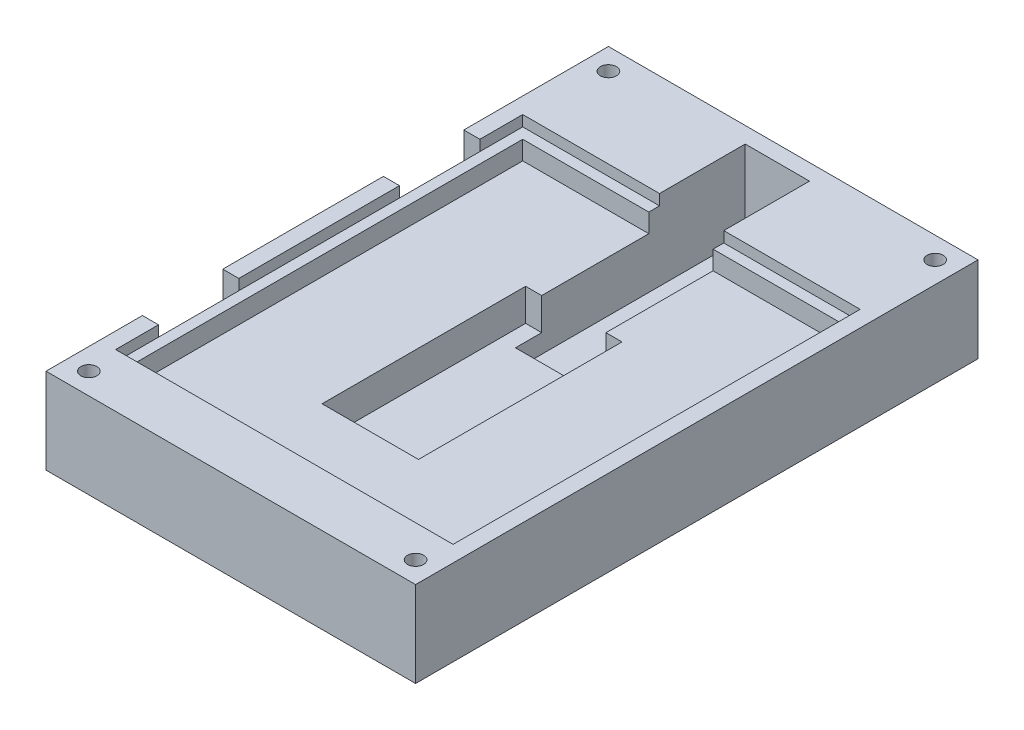
SolidWorks part; units mm, degrees
ref_plane "Front Plane" through (0, 0, 0) normal (0, 0, 1) x (1, 0, 0)
ref_plane "Top Plane" through (0, 0, 0) normal (0, 1, 0) x (1, 0, 0)
ref_plane "Right Plane" through (0, 0, 0) normal (1, 0, 0) x (0, 0, -1)
sketch "Sketch1" plane through (0, 0, 0) normal (0, 1, 0) x (1, 0, 0)
  line L1 (0, 0) -> (69, 0)
  line L2 (0, 0) -> (0, 105)
  line L3 (0, 105) -> (69, 105)
  line L4 (69, 0) -> (69, 105)
  dimension "D1" = 69
  dimension "D2" = 105
extrude "Boss-Extrude1" add sketch "Sketch1" along normal blind 16
sketch "Sketch2" plane through (0, 16, 0) normal (0, 1, 0) x (1, 0, 0)
  line L0 (0, 105) -> (0, 0) construction
  line L1 (3, 86) -> (66, 86)
  line L2 (3, 86) -> (3, 10)
  line L3 (3, 10) -> (66, 10)
  line L4 (66, 86) -> (66, 10)
  line L5 (0, 0) -> (69, 0) construction
  dimension "D1" = 63
  dimension "D2" = 76
  dimension "D3" = 3
  dimension "D4" = 10
extrude "Cut-Extrude1" cut sketch "Sketch2" against normal blind 2
sketch "Sketch3" plane through (0, 14, 0) normal (0, 1, 0) x (1, 0, 0)
  line L0 (3, 86) -> (3, 10) construction
  line L1 (5, 84) -> (64, 84)
  line L2 (5, 84) -> (5, 12)
  line L3 (5, 12) -> (64, 12)
  line L4 (64, 84) -> (64, 12)
  line L5 (66, 10) -> (66, 86) construction
  line L6 (66, 86) -> (3, 86) construction
  line L7 (3, 10) -> (66, 10) construction
  dimension "D1" = 2
  dimension "D2" = 2
  dimension "D3" = 2
  dimension "D4" = 2
extrude "Cut-Extrude2" cut sketch "Sketch3" against normal blind 3.5
sketch "Sketch4" plane through (0, 10.5, 0) normal (0, 1, 0) x (1, 0, 0)
  line L0 (64, 84) -> (5, 84) construction
  line L1 (25.54, 64) -> (43.54, 64)
  line L2 (25.54, 64) -> (25.54, 26)
  line L3 (25.54, 26) -> (43.54, 26)
  line L4 (43.54, 64) -> (43.54, 26)
  line L5 (64, 12) -> (64, 84) construction
  dimension "D1" = 18
  dimension "D2" = 38
  dimension "D3" = 20
  dimension "D4" = 20.46
extrude "Cut-Extrude3" cut sketch "Sketch4" against normal blind 6 contours L2 L3 L4 L1
sketch "Sketch5" plane through (0, 10.5, 0) normal (0, 1, 0) x (1, 0, 0)
  line L1 (28.54, 90.5747) -> (28.54, 59.1011)
  line L2 (28.54, 59.1011) -> (40.54, 59.1011)
  line L3 (40.54, 90.5747) -> (28.54, 90.5747)
  line L4 (40.54, 59.1011) -> (40.54, 90.5747)
  dimension "D1" = 12
extrude "Cut-Extrude4" cut sketch "Sketch5" against normal blind 9.5
sketch "Sketch6" plane through (0, 16, 0) normal (0, 1, 0) x (1, 0, 0)
  line L0 (69, 105) -> (0, 105) construction
  line L1 (28.54, 102) -> (40.54, 102)
  line L2 (28.54, 102) -> (28.54, 84)
  line L3 (28.54, 84) -> (40.54, 84)
  line L4 (40.54, 102) -> (40.54, 84)
  dimension "D1" = 3
extrude "Cut-Extrude5" cut sketch "Sketch6" against normal blind 15
sketch "Sketch7" plane through (0, 16, 0) normal (0, 1, 0) x (1, 0, 0)
  line L0 (0, 0) -> (69, 0) construction
  line L1 (0, 105) -> (0, 0) construction
  line L2 (69, 0) -> (69, 105) construction
  line L3 (69, 105) -> (0, 105) construction
  circle A0 centre (4, 4) radius 1.5
  circle A1 centre (65, 4) radius 1.5
  circle A2 centre (65, 101) radius 1.5
  circle A3 centre (4, 101) radius 1.5
  dimension "D1" = 3
  dimension "D2" = 3
  dimension "D3" = 3
  dimension "D4" = 3
  dimension "D5" = 4
  dimension "D6" = 4
  dimension "D7" = 4
  dimension "D8" = 4
  dimension "D9" = 4
  dimension "D10" = 4
  dimension "D11" = 4
  dimension "D12" = 4
extrude "Cut-Extrude6" cut sketch "Sketch7" against normal blind 10
ref_plane "Plane1" through (0, 0, -105) normal (0, 0, 1) x (1, 0, 0)
sketch "Sketch10" plane through (0, 0, 0) normal (-1, 0, 0) x (0, 0, 1)
  line L0 (-105, 16) -> (0, 16) construction
  line L1 (-90, 9.7321) -> (-91.5, 8.866)
  line L2 (-91.5, 8.866) -> (-91.5, 7.134)
  line L3 (-91.5, 7.134) -> (-90, 6.2679)
  line L4 (-90, 6.2679) -> (-88.5, 7.134)
  line L5 (-88.5, 7.134) -> (-88.5, 8.866)
  line L6 (-88.5, 8.866) -> (-90, 9.7321)
  line L7 (-52.5, 9.7321) -> (-54, 8.866)
  line L8 (-54, 8.866) -> (-54, 7.134)
  line L9 (-54, 7.134) -> (-52.5, 6.2679)
  line L10 (-52.5, 6.2679) -> (-51, 7.134)
  line L11 (-51, 7.134) -> (-51, 8.866)
  line L12 (-51, 8.866) -> (-52.5, 9.7321)
  line L13 (-15, 9.7321) -> (-16.5, 8.866)
  line L14 (-16.5, 8.866) -> (-16.5, 7.134)
  line L15 (-16.5, 7.134) -> (-15, 6.2679)
  line L16 (-15, 6.2679) -> (-13.5, 7.134)
  line L17 (-13.5, 7.134) -> (-13.5, 8.866)
  line L18 (-13.5, 8.866) -> (-15, 9.7321)
  line L19 (-105, -28.875) -> (-105, 28.875) construction
  line L20 (0, 16) -> (0, 0) construction
  line L21 (-90, 9.7321) -> (-90, 6.2679) construction
  line L22 (-88.5, 7.134) -> (-91.5, 8.866) construction
  line L23 (-54, 7.134) -> (-51, 8.866) construction
  line L24 (-54, 8.866) -> (-51, 7.134) construction
  line L25 (-16.5, 7.134) -> (-13.5, 8.866) construction
  line L26 (-16.5, 8.866) -> (-13.5, 7.134) construction
  circle A0 centre (-90, 8) radius 1.5 construction
  circle A1 centre (-52.5, 8) radius 1.5 construction
  circle A2 centre (-15, 8) radius 1.5 construction
  dimension "D1" = 8
  dimension "D2" = 8
  dimension "D3" = 8
  dimension "D4" = 15
  dimension "D5" = 15
  dimension "D6" = 52.5
  dimension "D7" = 3
  dimension "D8" = 3
  dimension "D9" = 3
extrude "Cut-Extrude7" cut sketch "Sketch10" against normal blind 10
sketch "Sketch11" plane through (10, 0, 0) normal (-1, 0, 0) x (0, 0, 1)
  line L0 (-88.5, 7.134) -> (-91.5, 8.866) construction
  line L1 (-91.5, 8.866) -> (-91.5, 7.134) construction
  line L2 (-54, 8.866) -> (-51, 7.134) construction
  line L3 (-88.5, 8.866) -> (-91.5, 7.134) construction
  line L4 (-16.5, 8.866) -> (-13.5, 7.134) construction
  point P4 (-90, 8)
  point P13 (-52.5, 8)
  point P18 (-15, 8)
sketch "Sketch13" plane through (0, 16, 0) normal (0, 1, 0) x (1, 0, 0)
  line L0 (0, 105) -> (0, 0) construction
  line L1 (0, 78) -> (3, 78)
  line L2 (0, 78) -> (0, 63)
  line L3 (0, 63) -> (3, 63)
  line L4 (3, 78) -> (3, 63)
  line L5 (3, 86) -> (3, 10) construction
  line L6 (28.54, 86) -> (3, 86) construction
  line L7 (3, 10) -> (66, 10) construction
  line L8 (3, 18) -> (0, 18)
  line L9 (3, 18) -> (3, 33)
  line L10 (3, 33) -> (0, 33)
  line L11 (0, 18) -> (0, 33)
  dimension "D1" = 8
  dimension "D2" = 15
  dimension "D3" = 8
  dimension "D4" = 15
extrude "Cut-Extrude8" cut sketch "Sketch13" against normal through all
